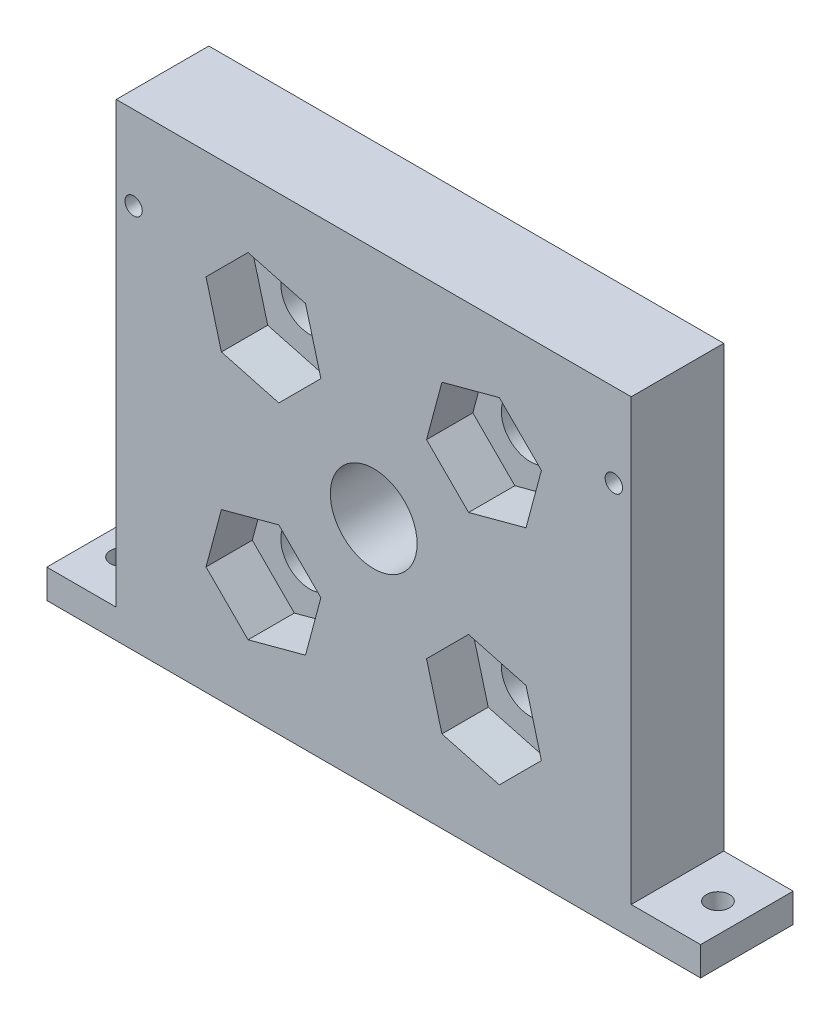
SolidWorks part; units mm, degrees
ref_plane "Plan de face" through (0, 0, 0) normal (0, 0, 1) x (1, 0, 0)
ref_plane "Plan de dessus" through (0, 0, 0) normal (0, 1, 0) x (1, 0, 0)
ref_plane "Plan de droite" through (0, 0, 0) normal (1, 0, 0) x (0, 0, -1)
sketch "Esquisse1" plane through (0, 0, 0) normal (0, 0, 1) x (1, 0, 0)
  line L0 (0, 0) -> (0, 20.2323) construction
  line L2 (-56.5, 0) -> (-56.5, 5) construction
  line L3 (-56.5, 5) -> (-44.5, 5) construction
  line L4 (-44.5, 13.3425) -> (-44.5, 72.3618) construction
  line L11 (-56.5, 0) -> (-35.792, 0) construction
  line L28 (-13.1159, 49.7073) -> (-44.5, 5) construction
  line L29 (-35.792, 0) -> (-21.7522, 20) construction
  line L30 (35.792, 0) -> (21.7522, 20) construction
  line L31 (13.1159, 49.7073) -> (44.5, 5) construction
  line L32 (56.5, 0) -> (35.792, 0) construction
  line L33 (56.5, 5) -> (44.5, 5) construction
  line L34 (56.5, 0) -> (56.5, 5) construction
  line L35 (-21.7522, 20) -> (21.7522, 20) construction
  line L36 (44.5, 5) -> (15.9887, 45.6149) construction
  line L37 (0, 40.5) -> (13.1159, 49.7073) construction
  line L49 (-44.5, 65.6296) -> (-44.5, 69.2189) construction
  line L50 (-44.5, 69.2189) -> (-40.9107, 69.2189) construction
  line L51 (-40.9107, 69.2189) -> (-13.1159, 49.7073) construction
  line L52 (-15.9887, 45.6149) -> (-44.5, 65.6296) construction
  line L54 (-44.5, 5) -> (-15.9887, 45.6149) construction
  line L55 (-13.1159, 49.7073) -> (-6.1385, 44.8092) construction
  line L56 (6.1385, 44.8092) -> (13.1159, 49.7073) construction
  line L57 (44.5, 65.6296) -> (44.5, 69.2189) construction
  line L58 (44.5, 69.2189) -> (40.9107, 69.2189) construction
  line L59 (15.9887, 45.6149) -> (44.5, 65.6296) construction
  line L60 (40.9107, 69.2189) -> (13.1159, 49.7073) construction
  line L61 (-17.0873, 35.3475) -> (-25.8445, 22.8728) construction
  line L62 (-25.8445, 22.8728) -> (-3.3233, 22.8728) construction
  line L63 (-21.7522, 20) -> (-29.9368, 25.7456) construction
  line L64 (-3.3233, 22.8728) -> (-3.3233, 25.8728) construction
  line L65 (-17.0873, 35.3475) -> (-14.0873, 35.3475) construction
  line L66 (0, 40.5) -> (0, 56.525) construction
  line L67 (17.0873, 35.3475) -> (14.0873, 35.3475) construction
  line L68 (3.3233, 22.8728) -> (3.3233, 25.8728) construction
  line L69 (25.8445, 22.8728) -> (3.3233, 22.8728) construction
  line L70 (17.0873, 35.3475) -> (25.8445, 22.8728) construction
  circle A1 centre (0, 40.5) radius 11.025 construction
  arc A3 (13.1159, 49.7073) -> (-13.1159, 49.7073) centre (0, 40.5) ccw construction
  circle A5 centre (0, 40.5) radius 7 construction
  arc A6 (-6.1385, 44.8092) -> (6.1385, 44.8092) centre (0, 40.5) ccw construction
  arc A7 (-3.3233, 25.8728) -> (-14.0873, 35.3475) centre (0, 40.5) cw construction
  arc A8 (3.3233, 25.8728) -> (14.0873, 35.3475) centre (0, 40.5) ccw construction
  point P17 (0, 20)
  dimension "D1" = 22.05
  dimension "D5" = 5
  dimension "D9" = 14
  dimension "D10" = 0.5
  dimension "D12" = 15
  dimension "D2" = 40.5
  dimension "D3" = 5
  dimension "D4" = 12
  dimension "D6" = 10
  dimension "D7" = 56.5
  dimension "D8" = 20
  dimension "D11" = 5
  dimension "D13" = 3
sketch "Esquisse2" plane through (0, 0, 0) normal (0, 0, 1) x (1, 0, 0)
  line L1 (-56.5, 0) -> (56.5, 0)
  line L5 (44.5, 5) -> (44.5, 81)
  line L6 (56.5, 5) -> (44.5, 5)
  line L7 (56.5, 0) -> (56.5, 5)
  line L10 (-19.0565, 59.5565) -> (19.0565, 21.4435) construction
  line L16 (-56.5, 0) -> (-56.5, 5)
  line L17 (-56.5, 5) -> (-44.5, 5)
  line L18 (-44.5, 5) -> (-44.5, 81)
  line L19 (-44.5, 81) -> (44.5, 81)
  line L20 (0, -200000) -> (0, 200020.2323) construction
  line L21 (0, 40.5) -> (-44.5, 40.5) construction
  line L22 (0, 81) -> (0, 40.5) construction
  line L23 (19.0565, 59.5565) -> (-19.0565, 21.4435) construction
  line L24 (5.6716, 15.1296) -> (25.3704, 34.8284) construction
  line L25 (-13.7639, 57.7781) -> (-17.2781, 54.2639) construction
  line L27 (-40.0636, 68.6243) -> (-42.9364, 64.532) construction
  line L28 (-40.9107, 69.2189) -> (-13.1159, 49.7073) construction
  line L29 (-15.9887, 45.6149) -> (-44.5, 65.6296) construction
  circle A1 centre (-19.0565, 21.4435) radius 5
  circle A2 centre (-19.0565, 59.5565) radius 5
  circle A3 centre (19.0565, 59.5565) radius 5
  circle A4 centre (19.0565, 21.4435) radius 5
  circle A5 centre (0, 40.5) radius 7 construction
  circle A6 centre (0, 40.5) radius 7 construction
  circle A7 centre (0, 40.5) radius 40.5 construction
  circle A8 centre (-41.5, 66.5781) radius 1.5
  circle A9 centre (41.5, 66.5781) radius 1.5
  circle A10 centre (0, 40.5) radius 7.5
  arc A11 (-6.1385, 44.8092) -> (6.1385, 44.8092) centre (0, 40.5) ccw construction
  point P23 (0, 0)
  point P29 (15.521, 24.979)
  point P41 (-15.521, 56.021)
  dimension "D1" = 10
  dimension "D3" = 3
  dimension "D4" = 3
  dimension "D2" = 43.9
extrude "Boss.-Extru.1" add sketch "Esquisse2" along normal blind 16
sketch "Esquisse3" plane through (0, 0, 0) normal (0, 0, 1) x (1, 0, 0)
  line L1 (-56.5, 0) -> (56.5, 0)
  line L2 (-56.5, 0) -> (-56.5, 5)
  line L3 (-56.5, 5) -> (56.5, 5)
  line L4 (56.5, 0) -> (56.5, 5)
sketch "Esquisse4" plane through (0, 5, 0) normal (0, 1, 0) x (1, 0, 0)
  line L1 (-56.5, -16) -> (-56.5, 0) construction
  line L2 (-56.5, -8) -> (56.5, -8) construction
  line L4 (0, 0) -> (0, -16) construction
  line L8 (-56.5, -16) -> (-56.5, 0) construction
  line L9 (56.5, -16) -> (56.5, 0) construction
  line L10 (-56.5, -16) -> (56.5, -16) construction
  circle A0 centre (-51.5, -8) radius 2
  circle A4 centre (51.5, -8) radius 2
  point P6 (0, 0)
  dimension "D1" = 4
  dimension "D3" = 5
extrude "Enlèv. mat.-Extru.1" cut sketch "Esquisse4" against normal through all
sketch "Esquisse5" plane through (0, 0, 16) normal (0, 0, 1) x (1, 0, 0)
  line L0 (13.1168, 27.3832) -> (-13.1168, 53.6168) construction
  line L1 (-12.198, 66.4151) -> (-21.5669, 68.9255) construction
  line L2 (-21.5669, 68.9255) -> (-28.4255, 62.0669) construction
  line L3 (-28.4255, 62.0669) -> (-25.9151, 52.698) construction
  line L4 (-25.9151, 52.698) -> (-16.5461, 50.1875) construction
  line L5 (-16.5461, 50.1875) -> (-9.6875, 57.0461) construction
  line L6 (-9.6875, 57.0461) -> (-12.198, 66.4151) construction
  line L7 (0, 81) -> (0, 0) construction
  line L8 (44.5, 81) -> (-44.5, 81) construction
  line L9 (0, 40.5) -> (-44.5, 40.5) construction
  line L10 (-44.5, 81) -> (-44.5, 5) construction
  line L11 (-21.7164, 69.4832) -> (-16.3967, 49.6299) construction
  line L12 (-21.7164, 69.4832) -> (-28.9832, 62.2164)
  line L13 (-28.9832, 62.2164) -> (-26.3233, 52.2897)
  line L14 (-26.3233, 52.2897) -> (-16.3967, 49.6299)
  line L15 (-16.3967, 49.6299) -> (-9.1299, 56.8967)
  line L16 (-9.1299, 56.8967) -> (-11.7897, 66.8233)
  line L17 (-11.7897, 66.8233) -> (-21.7164, 69.4832)
  line L18 (-21.7164, 11.5168) -> (-28.9832, 18.7836)
  line L19 (-11.7897, 14.1767) -> (-21.7164, 11.5168)
  line L20 (-9.1299, 24.1033) -> (-11.7897, 14.1767)
  line L21 (-16.3967, 31.3701) -> (-9.1299, 24.1033)
  line L22 (-26.3233, 28.7103) -> (-16.3967, 31.3701)
  line L23 (-28.9832, 18.7836) -> (-26.3233, 28.7103)
  line L24 (26.3233, 52.2897) -> (16.3967, 49.6299)
  line L25 (16.3967, 49.6299) -> (9.1299, 56.8967)
  line L26 (9.1299, 56.8967) -> (11.7897, 66.8233)
  line L27 (11.7897, 66.8233) -> (21.7164, 69.4832)
  line L28 (21.7164, 69.4832) -> (28.9832, 62.2164)
  line L29 (28.9832, 62.2164) -> (26.3233, 52.2897)
  line L30 (16.3967, 31.3701) -> (9.1299, 24.1033)
  line L31 (11.7897, 14.1767) -> (21.7164, 11.5168)
  line L32 (9.1299, 24.1033) -> (11.7897, 14.1767)
  line L33 (21.7164, 11.5168) -> (28.9832, 18.7836)
  line L34 (28.9832, 18.7836) -> (26.3233, 28.7103)
  line L35 (26.3233, 28.7103) -> (16.3967, 31.3701)
  circle A0 centre (-19.0565, 59.5565) radius 8.4 construction
  circle A1 centre (-19.0565, 59.5565) radius 8.9 construction
  circle A3 centre (0, 40.5) radius 18.55 construction
  dimension "D1" = 16.8
  dimension "D2" = 0.5
extrude "Enlèv. mat.-Extru.2" cut sketch "Esquisse5" against normal blind 8
